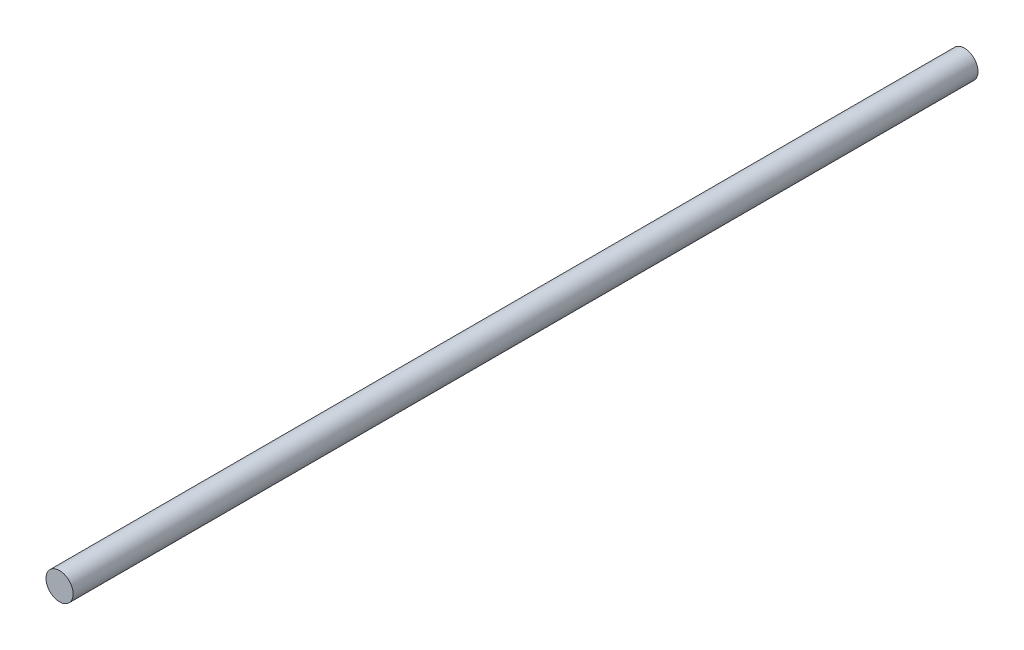
SolidWorks part; units mm, degrees
ref_plane "Alzado" through (0, 0, 0) normal (0, 0, 1) x (1, 0, 0)
ref_plane "Planta" through (0, 0, 0) normal (0, 1, 0) x (1, 0, 0)
ref_plane "Vista lateral" through (0, 0, 0) normal (1, 0, 0) x (0, 0, -1)
sketch "Croquis1" plane through (0, 0, 0) normal (0, 0, 1) x (1, 0, 0)
  circle A0 centre (0, 0) radius 0.762
  dimension "D1" = 1.524
extrude "Saliente-Extruir1" add sketch "Croquis1" along normal blind 50.8
